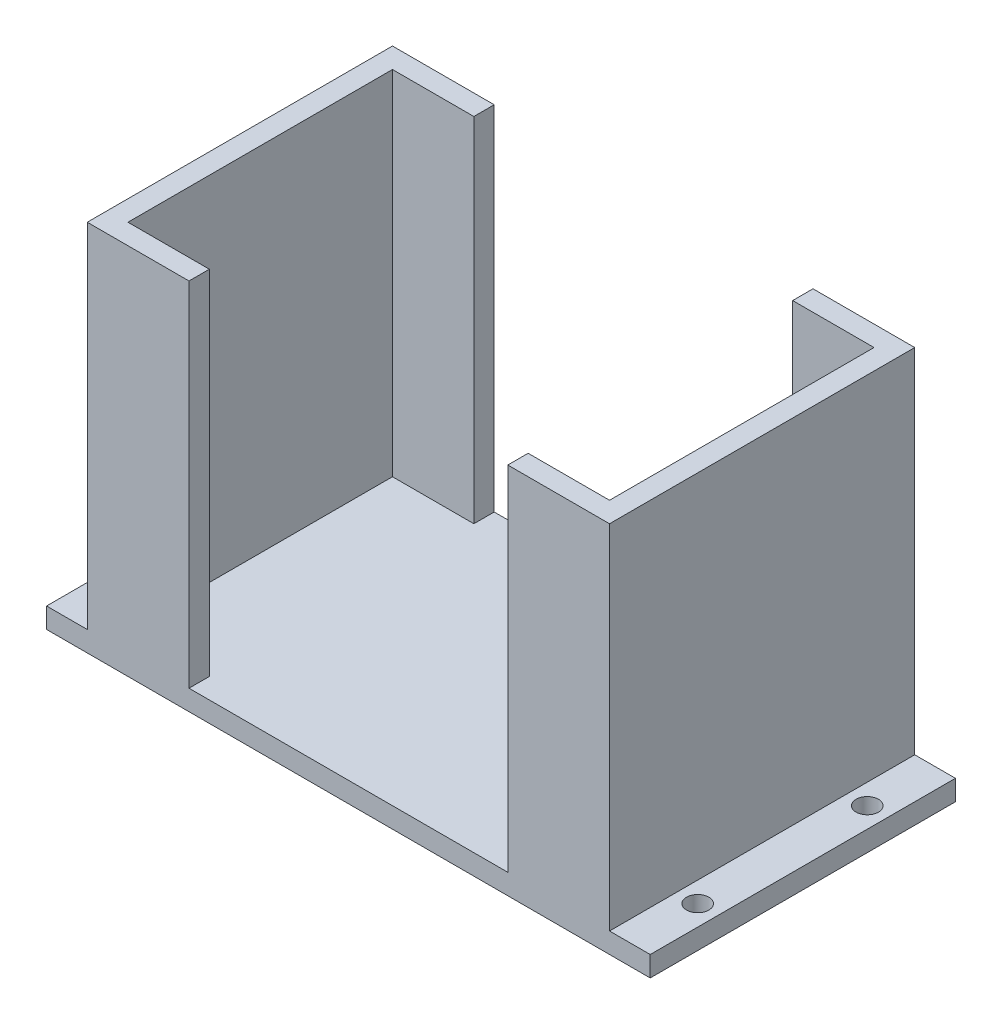
SolidWorks part; units mm, degrees
ref_plane "前视基准面" through (0, 0, 0) normal (0, 0, 1) x (1, 0, 0)
ref_plane "上视基准面" through (0, 0, 0) normal (0, 1, 0) x (1, 0, 0)
ref_plane "右视基准面" through (0, 0, 0) normal (1, 0, 0) x (0, 0, -1)
sketch "草图1" plane through (0, 0, 0) normal (0, 1, 0) x (1, 0, 0)
  line L0 (0, 0) -> (0, 22.5)
  line L1 (-38.5, 22.5) -> (38.5, 22.5)
  line L2 (-38.5, 22.5) -> (-38.5, -22.5)
  line L3 (-38.5, -22.5) -> (38.5, -22.5)
  line L4 (38.5, 22.5) -> (38.5, -22.5)
  line L5 (-38.5, 22.5) -> (38.5, -22.5) construction
  line L6 (-38.5, -22.5) -> (38.5, 22.5) construction
  line L7 (-35.5, 19.5) -> (35.5, 19.5)
  line L8 (-35.5, 19.5) -> (-35.5, -19.5)
  line L9 (-35.5, -19.5) -> (35.5, -19.5)
  line L10 (35.5, 19.5) -> (35.5, -19.5)
  line L11 (-35.5, 19.5) -> (35.5, -19.5) construction
  line L12 (-35.5, -19.5) -> (35.5, 19.5) construction
  line L13 (-38.5, 22.5) -> (-23.5, 22.5)
  line L14 (-23.5, 22.5) -> (-23.5, 19.5)
  line L15 (0, 0) -> (-38.5, 0)
  line L16 (-23.5, -22.5) -> (-23.5, -19.5)
  line L17 (23.5, 22.5) -> (23.5, 19.5)
  line L18 (23.5, -22.5) -> (23.5, -19.5)
  point P0 (0, 0)
  point P6 (0, 0)
  dimension "D1" = 77
  dimension "D2" = 3
  dimension "D3" = 45
  dimension "D4" = 3
  dimension "D5" = 15
extrude "凸台-拉伸1" add sketch "草图1" along normal blind 55 contours L15 L8 L7 L14 L1 L2 | L3 L16 L9 L8 L15 L2 | L18 L3 L4 L1 L17 L7 L10 L9
sketch "草图3" plane through (0, 0, 0) normal (0, -1, 0) x (1, 0, 0)
  line L0 (23.5, 19.5) -> (35.5, 19.5) construction
  line L1 (-35.5, -19.5) -> (35.5, -19.5)
  line L2 (-35.5, -19.5) -> (-35.5, 19.5)
  line L3 (-35.5, 19.5) -> (35.5, 19.5)
  line L4 (35.5, -19.5) -> (35.5, 19.5)
  line L5 (35.5, -19.5) -> (35.5, 19.5) construction
  line L6 (23.5, 22.5) -> (23.5, 19.5) construction
  line L7 (-23.5, 19.5) -> (23.5, 19.5)
  line L8 (-23.5, 19.5) -> (-23.5, 22.5)
  line L9 (-23.5, 22.5) -> (23.5, 22.5)
  line L10 (23.5, 19.5) -> (23.5, 22.5)
  line L12 (-23.5, -19.5) -> (23.5, -19.5)
  line L13 (-23.5, -19.5) -> (-23.5, -22.5)
  line L14 (-23.5, -22.5) -> (23.5, -22.5)
  line L15 (23.5, -19.5) -> (23.5, -22.5)
  line M3 (-23.5, -22.5) -> (-23.5, -19.5)
  line M4 (-23.5, -19.5) -> (-35.5, -19.5)
  line M5 (-35.5, -19.5) -> (-35.5, 19.5)
  line M6 (-35.5, 19.5) -> (-23.5, 19.5)
  line M7 (-23.5, 19.5) -> (-23.5, 22.5)
extrude "凸台-拉伸2" add sketch "草图3" against normal blind 3 contours L3 L10 L9 M7 | L1 L4 L3 M6 M5 M4 | L15 L1 L14 M3
sketch "草图4" plane through (38.5, 0, 0) normal (1, 0, 0) x (0, 0, -1)
  line L0 (22.5, 55) -> (22.5, 0) construction
  line L1 (-22.5, 0) -> (22.5, 0)
  line L2 (-22.5, 0) -> (-22.5, 3)
  line L3 (-22.5, 3) -> (22.5, 3)
  line L4 (22.5, 0) -> (22.5, 3)
extrude "凸台-拉伸3" add sketch "草图4" along normal blind 6
sketch "草图6" plane through (0, 3, 0) normal (0, 1, 0) x (1, 0, 0)
  line L0 (44.5, -22.5) -> (38.5, -22.5) construction
  line L1 (41.5, -22.5) -> (41.5, -12.5)
  line L2 (44.5, 22.5) -> (38.5, 22.5) construction
  line L3 (41.5, 22.5) -> (41.5, 12.5)
  circle A0 centre (41.5, -12.5) radius 1.65
  circle A1 centre (41.5, 12.5) radius 1.65
  dimension "D1" = 3.3
  dimension "D2" = 25
extrude "切除-拉伸1" cut sketch "草图6" against normal blind 6
sketch "草图7" plane through (-38.5, 0, 0) normal (-1, 0, 0) x (0, 0, 1)
  line L0 (22.5, 55) -> (22.5, 0) construction
  line L1 (-22.5, 0) -> (22.5, 0)
  line L2 (-22.5, 0) -> (-22.5, 3)
  line L3 (-22.5, 3) -> (22.5, 3)
  line L4 (22.5, 0) -> (22.5, 3)
extrude "凸台-拉伸4" add sketch "草图7" along normal blind 6
sketch "草图8" plane through (0, 3, 0) normal (0, 1, 0) x (1, 0, 0)
  line L0 (-44.5, 22.5) -> (-38.5, 22.5) construction
  line L1 (-41.5, 22.5) -> (-41.5, 12.5)
  line L2 (-44.5, -22.5) -> (-38.5, -22.5) construction
  line L3 (-41.5, -22.5) -> (-41.5, -12.5)
  circle A0 centre (-41.5, 12.5) radius 1.65
  circle A1 centre (-41.5, -12.5) radius 1.65
  point P10 (-41.5, 8.397)
  dimension "D1" = 25
  dimension "D2" = 3.3
extrude "切除-拉伸2" cut sketch "草图8" against normal blind 6
